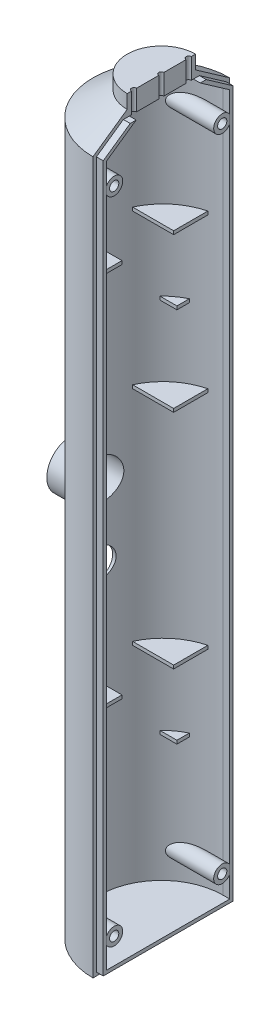
SolidWorks part; units mm, degrees
ref_plane "前视基准面" through (0, 0, 0) normal (0, 0, 1) x (1, 0, 0)
ref_plane "上视基准面" through (0, 0, 0) normal (0, 1, 0) x (1, 0, 0)
ref_plane "右视基准面" through (0, 0, 0) normal (1, 0, 0) x (0, 0, -1)
other "Configuration Table"
sketch "草图1" plane through (0, 0, 0) normal (0, 0, 1) x (1, 0, 0)
  line L0 (0, 0) -> (10, 0)
  line L3 (20, -7) -> (20, -215)
  line L4 (0, 0) -> (0, -215)
  line L5 (0, -215) -> (20, -215)
  line L7 (20, -7) -> (10, 0)
  dimension "D1" = 10
  dimension "D2" = 208
  dimension "D3" = 20
  dimension "D5" = 215
revolve "旋转1" add sketch "草图1" angle 360 about L4
sketch "草图2" plane through (0, 0, 0) normal (0, 1, 0) x (1, 0, 0)
  line L1 (0, -23.7241) -> (24.0136, -23.7241)
  line L2 (0, -23.7241) -> (0, 24.0949)
  line L3 (0, 24.0949) -> (24.0136, 24.0949)
  line L4 (24.0136, -23.7241) -> (24.0136, 24.0949)
extrude "切除-拉伸1" cut sketch "草图2" against normal blind 242
shell "抽壳1" thickness 2
sketch "草图3" plane through (0, 0, 0) normal (1, 0, 0) x (0, 0, -1)
  line L6 (-9.3696, -2) -> (-11.1133, -2)
  line L7 (9.3696, -2) -> (11.1133, -2)
  line L22 (9.3696, -2) -> (18, -8.0413)
  line L23 (18, -8.0413) -> (18, -213)
  line L24 (18, -213) -> (-18, -213)
  line L25 (-18, -213) -> (-18, -8.0413)
  line L26 (-18, -8.0413) -> (-9.3696, -2)
  line L27 (-19, -214) -> (19, -214)
  line L28 (19, -214) -> (19, -7.5207)
  line L29 (-19, -7.5207) -> (-19, -214)
  line L30 (19, -7.5207) -> (9.6848, -1)
  line L31 (9.6848, -1) -> (-9.6848, -1)
  line L32 (-9.6848, -1) -> (-19, -7.5207)
  line L33 (-19, -214) -> (19, -214)
  line L34 (19, -214) -> (19, -7.5207)
  line L35 (-19, -7.5207) -> (-19, -214)
  line L36 (19, -7.5207) -> (11.1133, -2)
  line L38 (-11.1133, -2) -> (-19, -7.5207)
  dimension "D1" = 1
extrude "凸台-拉伸1" add sketch "草图3" along normal blind 2
ref_plane "基准面1" through (0, -152.5, 0) normal (0, 1, 0) x (1, 0, 0)
sketch "草图4" plane through (0, -152.5, 0) normal (0, 1, 0) x (1, 0, 0)
  line L0 (-3.9647, 17.5579) -> (-3.9647, 7.5579)
  line L1 (-3.9647, -17.5579) -> (-3.9647, -7.5579)
  line L3 (-3.9647, 7.5579) -> (-15.9647, 7.5579)
  line L4 (-3.9647, -7.5579) -> (-15.9647, -7.5579)
  circle A0 centre (0, 0) radius 18 construction
  arc A1 (-3.9647, 17.5579) -> (-15.9647, 7.5579) centre (0.5003, 0) ccw
  arc A2 (-15.9647, -7.5579) -> (-3.9647, -17.5579) centre (0.5003, 0) ccw
  dimension "D1" = 10
  dimension "D2" = 10
  dimension "D3" = 12
  dimension "D4" = 12
extrude "凸台-拉伸2" add sketch "草图4" along normal blind 1
sketch "草图6" plane through (2, 0, 0) normal (1, 0, 0) x (0, 0, -1)
  line L0 (18, -8.0413) -> (18, -213) construction
  line L1 (18, -213) -> (-18, -213) construction
  line L2 (-18, -213) -> (-18, -8.0413) construction
  circle A0 centre (15.8, -205.5) radius 2.5
  circle A1 centre (-15.8, -205.5) radius 2.5
  circle A2 centre (-15.8, -205.5) radius 1.35
  circle A3 centre (15.8, -205.5) radius 1.35
  dimension "D1" = 5
  dimension "D4" = 5
  dimension "D7" = 2.7
  dimension "D8" = 2.7
  dimension "D2" = 2.2
  dimension "D3" = 7.5
  dimension "D5" = 2.2
  dimension "D6" = 7.5
extrude "凸台-拉伸7" add sketch "草图6" against normal up to next separate body
pattern_linear "阵列(线性)1" count 2 spacing 190 along (0, 1, 0) of "凸台-拉伸7"
ref_plane "基准面2" through (-20, 0, 0) normal (1, 0, 0) x (0, 0, -1)
sketch "草图8" plane through (-20, 0, 0) normal (1, 0, 0) x (0, 0, -1)
  line L0 (-10, 0) -> (10, 0) construction
  line L1 (-8, -135) -> (8, -135)
  line L2 (-8, -135) -> (-8, -100)
  line L3 (-8, -100) -> (8, -100)
  line L4 (8, -135) -> (8, -100)
  line L5 (-8, -135) -> (8, -100) construction
  line L6 (-8, -100) -> (8, -135) construction
  point P0 (0, -117.5)
  dimension "D1" = 16
  dimension "D2" = 35
  dimension "D3" = 100
  dimension "D4" = 8
extrude "切除-拉伸3" cut sketch "草图8" along normal blind 1.5
sketch "草图9" plane through (-18.5, 0, 0) normal (-1, 0, 0) x (0, 0, 1)
  line L0 (-7.5993, -100) -> (7.5993, -100) construction
  circle A0 centre (0, -108) radius 6
  circle A1 centre (0, -129) radius 4.25
  circle A2 centre (0, -119) radius 1.5
  dimension "D1" = 12
  dimension "D2" = 8.5
  dimension "D6" = 3
  dimension "D3" = 21
  dimension "D4" = 8
  dimension "D5" = 10
extrude "切除-拉伸4" cut sketch "草图9" against normal blind 4
sketch "草图10" plane through (0, 0, 0) normal (0, 1, 0) x (1, 0, 0)
  line L0 (0, 10) -> (0, -10)
  arc A0 (0, 10) -> (0, -10) centre (0, 0) ccw
extrude "凸台-拉伸8" add sketch "草图10" along normal blind 4
sketch "草图11" plane through (0, 4, 0) normal (0, 1, 0) x (1, 0, 0)
  line L0 (0, -10) -> (0, 10) construction
  circle A0 centre (0, 0) radius 0.75
  circle A1 centre (0, 8) radius 0.75
  circle A2 centre (0, -8) radius 0.75
  dimension "D3" = 1.5
  dimension "D4" = 1.5
  dimension "D5" = 1.5
  dimension "D1" = 8
  dimension "D2" = 8
extrude "切除-拉伸5" cut sketch "草图11" against normal blind 6
ref_plane "基准面3" through (0, -65, 0) normal (0, -1, 0) x (-1, 0, 0)
sketch "草图12" plane through (0, -65, 0) normal (0, -1, 0) x (-1, 0, 0)
  line L0 (7.9518, 12.5) -> (12.9518, 12.5)
  line L1 (7.9518, -12.5) -> (12.9518, -12.5)
  line L2 (7.9518, 12.5) -> (7.9518, 16.5527)
  line L3 (7.9518, -12.5) -> (7.9518, -16.0559)
  arc A0 (0, -18) -> (0, 18) centre (0, 0) ccw construction
  arc A1 (12.9518, 12.5) -> (7.9518, 16.5527) centre (8.8094, 12.5) ccw
  arc A2 (7.9518, -16.0559) -> (12.9518, -12.5) centre (7.9518, -10.7626) ccw
  dimension "D1" = 25
  dimension "D2" = 12.5
  dimension "D3" = 5
  dimension "D4" = 5
extrude "凸台-拉伸9" add sketch "草图12" along normal blind 1
pattern_linear "阵列(线性)2" count 2 spacing 110 along (0, -1, 0) of "凸台-拉伸9"
sketch "草图13" plane through (-18.5, 0, 0) normal (-1, 0, 0) x (0, 0, 1)
  circle A0 centre (0, -108) radius 6
  circle A1 centre (0, -108) radius 7
  dimension "D1" = 14
  dimension "D2" = 12
extrude "凸台-拉伸10" add sketch "草图13" along normal blind 8
pattern_linear "阵列(线性)5" count 2 spacing 110 along (0, 1, 0) of "凸台-拉伸2"
pattern_linear "阵列(线性)6" count 2 spacing 65 along (0, 1, 0) of bodies 116
